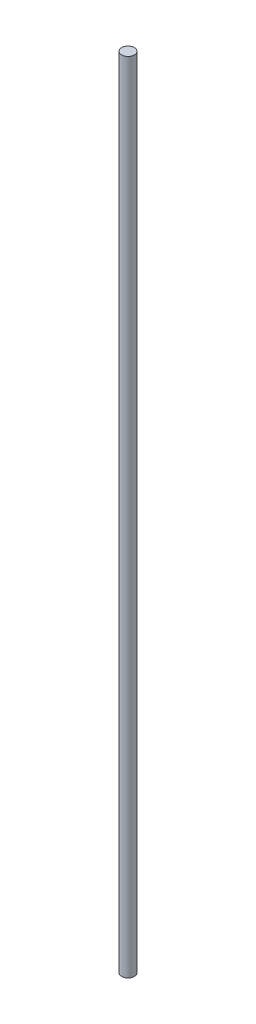
SolidWorks part; units mm, degrees
ref_plane "Front Plane" through (0, 0, 0) normal (0, 0, 1) x (1, 0, 0)
ref_plane "Top Plane" through (0, 0, 0) normal (0, 1, 0) x (1, 0, 0)
ref_plane "Right Plane" through (0, 0, 0) normal (1, 0, 0) x (0, 0, -1)
sketch "Sketch1" plane through (0, 0, 0) normal (0, 1, 0) x (1, 0, 0)
  circle A0 centre (0, 0) radius 0.5
  dimension "D1" = 1
extrude "Boss-Extrude1" add sketch "Sketch1" along normal blind 62.5 contours A0
